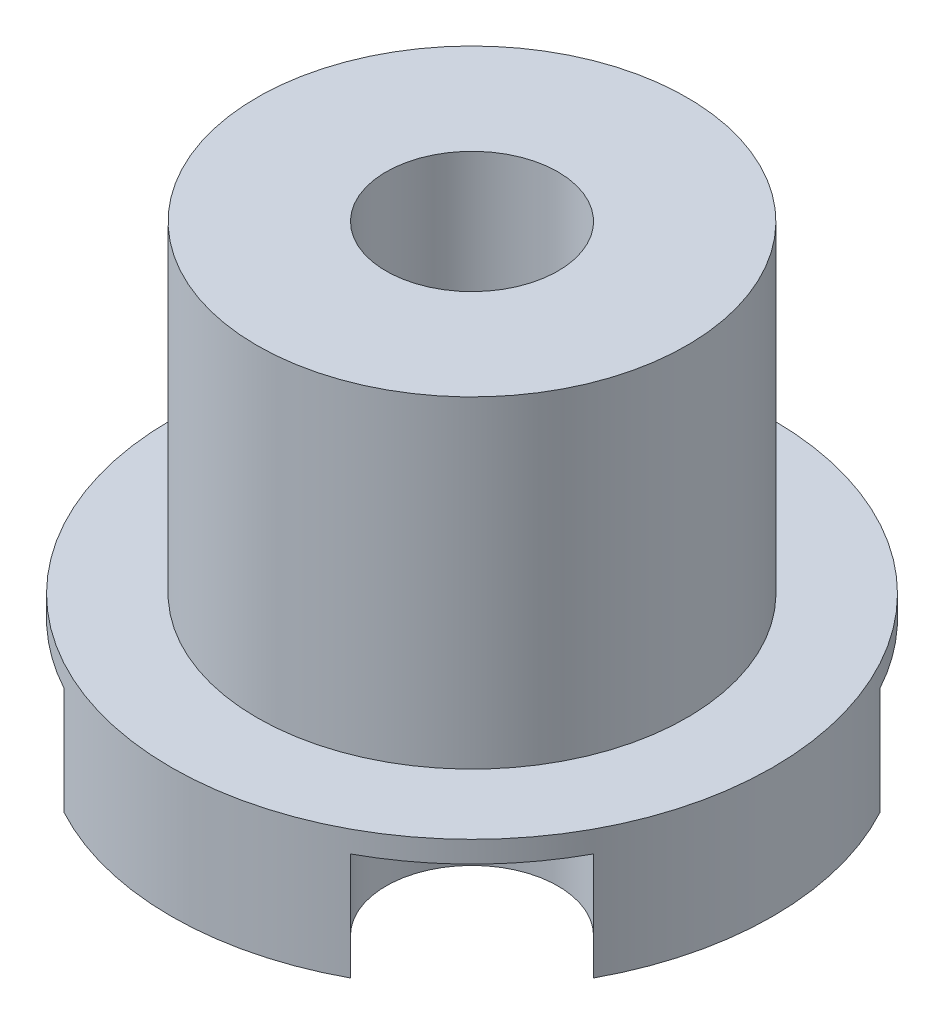
SolidWorks part; units mm, degrees
ref_plane "Спереди" through (0, 0, 0) normal (0, 0, 1) x (1, 0, 0)
ref_plane "Сверху" through (0, 0, 0) normal (0, 1, 0) x (1, 0, 0)
ref_plane "Справа" through (0, 0, 0) normal (1, 0, 0) x (0, 0, -1)
sketch "Эскиз1" plane through (0, 0, 0) normal (0, 1, 0) x (1, 0, 0)
  circle A0 centre (0, 0) radius 14
  dimension "D1" = 28
extrude "Бобышка-Вытянуть1" add sketch "Эскиз1" along normal blind 6
sketch "Эскиз2" plane through (0, 6, 0) normal (0, 1, 0) x (1, 0, 0)
  circle A0 centre (0, 0) radius 10
  circle A1 centre (0, 0) radius 14 construction
  dimension "D1" = 4
extrude "Бобышка-Вытянуть2" add sketch "Эскиз2" along normal blind 15
sketch "Эскиз3" plane through (0, 0, 0) normal (0, -1, 0) x (1, 0, 0)
  line L0 (0, 14) -> (0, -14) construction
  line L1 (-14, 0) -> (14, 0) construction
  line L2 (0, 0) -> (-9.8995, 9.8995) construction
  line L3 (0, 0) -> (9.8995, 9.8995) construction
  line L4 (0, 0) -> (-9.8995, -9.8995) construction
  line L5 (0, 0) -> (9.8995, -9.8995) construction
  circle A0 centre (0, 0) radius 14 construction
  circle A1 centre (-8, 0) radius 1
  circle A2 centre (8, 0) radius 1
  circle A3 centre (0, 9.5) radius 1
  circle A4 centre (0, -9.5) radius 1
  circle A5 centre (0, 0) radius 11 construction
  circle A6 centre (-7.7782, 7.7782) radius 4
  circle A7 centre (7.7782, 7.7782) radius 4
  circle A8 centre (7.7782, -7.7782) radius 4
  circle A9 centre (-7.7782, -7.7782) radius 4
  dimension "D1" = 19
  dimension "D2" = 16
  dimension "D3" = 8
  dimension "D4" = 9.5
  dimension "D5" = 2
  dimension "D6" = 2
  dimension "D7" = 2
  dimension "D8" = 2
  dimension "D13" = 8
  dimension "D15" = 8
  dimension "D16" = 8
  dimension "D17" = 8
  dimension "D9" = 45
  dimension "D10" = 45
  dimension "D11" = 45
  dimension "D12" = 45
extrude "Вырез-Вытянуть1" cut sketch "Эскиз3" against normal blind 5
sketch "Эскиз4" plane through (0, 0, 0) normal (0, -1, 0) x (1, 0, 0)
  line L0 (-26.1624, 20.5055) -> (4.9492, -10.606) construction
  line L1 (-26.1624, 20.5055) -> (-20.5055, 26.1624) construction
  line L2 (4.9492, -10.606) -> (10.606, -4.9492) construction
  line L3 (-20.5055, 26.1624) -> (10.606, -4.9492) construction
  line L4 (-26.1624, 20.5055) -> (10.606, -4.9492) construction
  line L5 (4.9492, -10.606) -> (-20.5055, 26.1624) construction
  line L6 (0, 14) -> (0, 0) construction
  line L7 (0, 0) -> (-7.7782, 7.7782) construction
  line L8 (-4.9497, 10.6066) -> (-10.6066, 4.9497)
  line L9 (-10.6066, 4.9497) -> (-15.3332, 9.6764)
  line L10 (-15.3332, 9.6764) -> (-9.6764, 15.3332)
  line L11 (-9.6764, 15.3332) -> (-4.9497, 10.6066)
  arc A0 (7.576, 11.7731) -> (-7.576, 11.7731) centre (0, 0) ccw construction
  point P1 (-7.7782, 7.7782)
  dimension "D1" = 4
extrude "Вырез-Вытянуть2" cut sketch "Эскиз4" against normal blind 5
pattern_circular "Круговой массив1" count 4 over 360 about axis through (0, 0, 0) along (0, 1, 0) of "Вырез-Вытянуть2"
sketch "Эскиз5" plane through (0, 0, 0) normal (0, -1, 0) x (1, 0, 0)
  circle A0 centre (0, 0) radius 4
  dimension "D1" = 8
extrude "Вырез-Вытянуть3" cut sketch "Эскиз5" against normal through all
